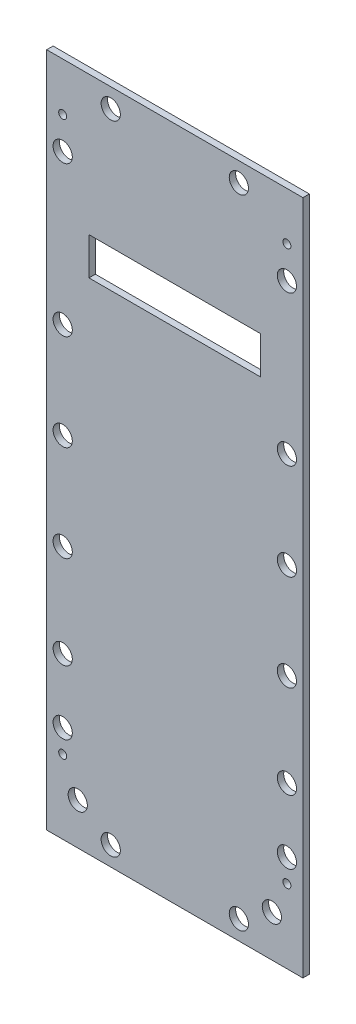
SolidWorks part; units mm, degrees
ref_plane "Front Plane" through (0, 0, 0) normal (0, 0, 1) x (1, 0, 0)
ref_plane "Top Plane" through (0, 0, 0) normal (0, 1, 0) x (1, 0, 0)
ref_plane "Right Plane" through (0, 0, 0) normal (1, 0, 0) x (0, 0, -1)
sketch "Sketch2" plane through (0, 0, 0) normal (0, 0, 1) x (1, 0, 0)
  line L0 (0, 0) -> (0, 211)
  line L1 (0, 211) -> (80, 211)
  line L2 (80, 211) -> (80, 0)
  line L3 (80, 0) -> (0, 0)
  line L4 (66.8, 167.6) -> (13.2, 167.6)
  line L6 (66.8, 167.6) -> (66.8, 155.9)
  line L8 (13.2, 167.6) -> (13.2, 155.9)
  line L9 (13.2, 155.9) -> (66.8, 155.9)
  dimension "D1" = 211
  dimension "D2" = 80
  dimension "D3" = 53.6
  dimension "D4" = 11.7
  dimension "D5" = 43.4
  dimension "D6" = 13.2
extrude "Boss-Extrude1" add sketch "Sketch2" along normal blind 2
sketch "Sketch3" plane through (0, 0, 0) normal (0, 0, -1) x (-1, 0, 0)
  line L0 (-80, 196) -> (0, 196) construction
  line L1 (-80, 0) -> (-80, 211) construction
  line L2 (0, 211) -> (0, 0) construction
  line L3 (-80, 23) -> (0, 23) construction
  line L4 (-75, 211) -> (-75, 0) construction
  line L5 (-80, 211) -> (0, 211) construction
  line L6 (0, 0) -> (-80, 0) construction
  line L7 (-5, 211) -> (-5, 0) construction
  line L8 (-40, 211) -> (-40, 0) construction
  dimension "D1" = 23
  dimension "D2" = 15
  dimension "D3" = 35
  dimension "70" = 70
hole_wizard "M3x0.5 Tapped Hole1" positions "Sketch4" profile "Sketch6" tap size "M3x0.5" standard "ANSI Metric"
sketch "Sketch4" plane through (0, 0, 0) normal (0, 0, -1) x (-1, 0, 0)
  line L0 (-80, 196) -> (0, 196) construction
  line L1 (-75, 211) -> (-75, 0) construction
  line L2 (-5, 211) -> (-5, 0) construction
  line L3 (-80, 23) -> (0, 23) construction
  point P0 (-75, 196)
  point P6 (-5, 196)
  point P10 (-75, 23)
  point P14 (-5, 23)
sketch "Sketch6" plane through (75, 196, 0) normal (1, 0, 0) x (0, 1, 0)
  line L0 (0, 0) -> (0, 10.7511)
  line L1 (0, 10.7511) -> (1.25, 10)
  line L2 (1.25, 10) -> (1.25, 0)
  line L5 (1.25, 0) -> (0, 0)
  line L10 (0, 10.7511) -> (-1.25, 10) construction
  line L11 (0, -6.35) -> (0, 107.95) construction
  dimension "Tap Drill Dia." = 2.5
  dimension "Tap Drill Depth" = 10
  dimension "Drill Angle" = 118
sketch "Sketch7" plane through (0, 0, 0) normal (0, 0, -1) x (-1, 0, 0)
  line L0 (-75, 211) -> (-75, 0) construction
  line L1 (-80, 211) -> (0, 211) construction
  line L2 (0, 0) -> (-80, 0) construction
  line L3 (-5, 211) -> (-5, 0) construction
  line L4 (-40, 211) -> (-40, 0) construction
  line L5 (-80, 0) -> (-80, 211) construction
  line L6 (0, 211) -> (0, 0) construction
  circle A0 centre (-75, 186) radius 3
  circle A1 centre (-75, 139.2) radius 3
  circle A2 centre (-75, 109.2) radius 3
  circle A3 centre (-75, 79.2) radius 3
  circle A4 centre (-75, 50.2) radius 3
  circle A5 centre (-75, 30.2) radius 3
  circle A6 centre (-5, 186) radius 3
  circle A7 centre (-5, 139.2) radius 3
  circle A8 centre (-5, 109.2) radius 3
  circle A9 centre (-5, 79.2) radius 3
  circle A10 centre (-5, 50.2) radius 3
  circle A11 centre (-5, 30.2) radius 3
  circle A12 centre (-70.3, 13) radius 3
  circle A13 centre (-60, 205) radius 3
  circle A14 centre (-20, 205) radius 3
  circle A15 centre (-60, 6) radius 3
  circle A16 centre (-20, 6) radius 3
  circle A17 centre (-9.7, 13) radius 3
  dimension "D4" = 6
  dimension "D10" = 40
  dimension "D1" = 70
  dimension "D2" = 35
  dimension "D3" = 25
  dimension "D5" = 46.8
  dimension "D6" = 30
  dimension "D7" = 30
  dimension "D8" = 29
  dimension "D9" = 20
  dimension "D11" = 20
  dimension "D12" = 6
  dimension "D13" = 6
  dimension "D14" = 9.7
  dimension "D15" = 9.7
  dimension "D16" = 13
extrude "Cut-Extrude1" cut sketch "Sketch7" against normal up to surface (2 mm away) up to face at (73.75, 196, 2)
